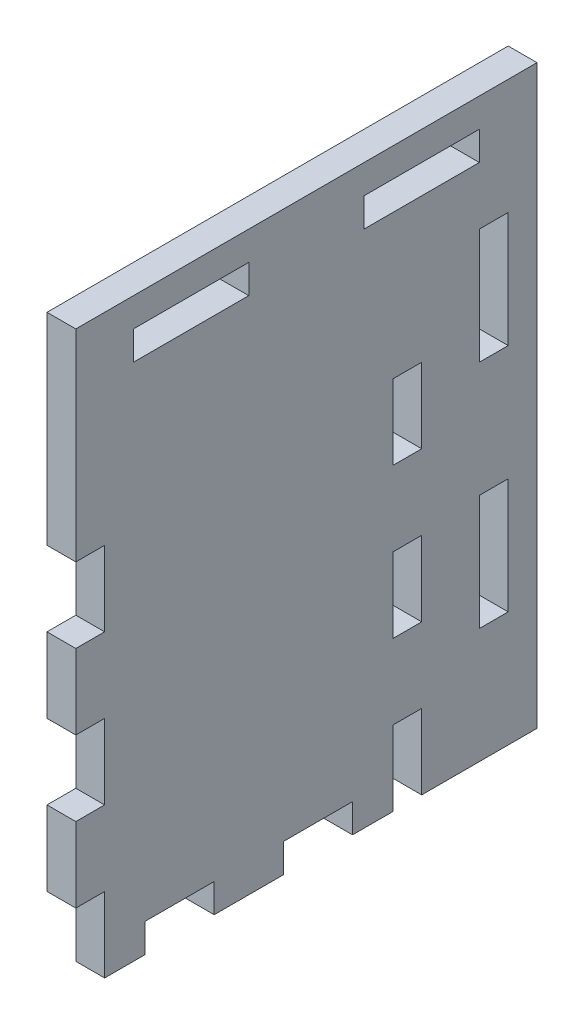
SolidWorks part; units mm, degrees
ref_plane "Plan de face" through (0, 0, 0) normal (0, 0, 1) x (1, 0, 0)
ref_plane "Plan de dessus" through (0, 0, 0) normal (0, 1, 0) x (1, 0, 0)
ref_plane "Plan de droite" through (0, 0, 0) normal (1, 0, 0) x (0, 0, -1)
sketch "Esquisse1" plane through (0, 0, 0) normal (1, 0, 0) x (0, 0, -1)
  line L0 (0, 0) -> (0, 35)
  line L2 (0, 0) -> (0, -65)
  line L3 (0, -65) -> (60, -65)
  line L4 (60, 0) -> (60, -65)
  line L5 (0, 35) -> (45, 35)
  line L7 (45, 0) -> (60, 0)
  line L8 (45, 0) -> (45, 35)
  dimension "D1" = 60
  dimension "D2" = 65
  dimension "D3" = 35
  dimension "D4" = 15
extrude "Boss.-Extru.1" add sketch "Esquisse1" along normal blind 5
sketch "Esquisse2" plane through (5, 0, 0) normal (1, 0, 0) x (0, 0, -1)
  line L0 (0, -65) -> (60, -65) construction
  line L1 (12, -65) -> (24, -65)
  line L2 (12, -65) -> (12, -60)
  line L3 (12, -60) -> (24, -60)
  line L4 (24, -65) -> (24, -60)
  line L5 (0, -65) -> (60, -65) construction
  line L6 (0, 35) -> (0, -65) construction
  dimension "D1" = 60
  dimension "D2" = 12
  dimension "D3" = 5
  dimension "D4" = 12
extrude "Enlèv. mat.-Extru.1" cut sketch "Esquisse2" against normal blind 5
pattern_linear "Répétition linéaire1" count 2 spacing 24 along (0, 0, -1) of "Enlèv. mat.-Extru.1"
ref_plane "Plan1" through (0, 0, -30) normal (0, 0, 1) x (1, 0, 0)
sketch "Esquisse4" plane through (5, 0, 0) normal (1, 0, 0) x (0, 0, -1)
  line L0 (60, 0) -> (60, -65) construction
  line L1 (0, -65) -> (5, -65)
  line L2 (0, -65) -> (0, -52)
  line L3 (0, -52) -> (5, -52)
  line L4 (5, -65) -> (5, -52)
  dimension "D3" = 5
  dimension "D1" = 65
  dimension "D2" = 13
extrude "Enlèv. mat.-Extru.2" cut sketch "Esquisse4" against normal blind 5
pattern_linear "Répétition linéaire2" count 3 spacing 26 along (0, 1, 0) of "Enlèv. mat.-Extru.2"
mirror "Symétrie1" about plane through (0, 0, -30) normal (0, 0, 1) of "Répétition linéaire2", "Enlèv. mat.-Extru.2"
sketch "Esquisse5" plane through (5, 0, 0) normal (1, 0, 0) x (0, 0, -1)
  line L0 (45, 0) -> (60, 0)
  line L2 (60, 0) -> (60, -65)
  line L3 (60, -65) -> (80, -65)
  line L5 (45, 0) -> (45, 35)
  line L6 (45, 35) -> (80, 35)
  line L8 (80, -65) -> (80, 35)
  line L9 (48, -65) -> (55, -65) construction
  line L10 (60, -52) -> (60, -39) construction
  dimension "D1" = 20
extrude "Boss.-Extru.3" add sketch "Esquisse5" against normal blind 5
ref_plane "Plan2" through (0, 0, -40) normal (0, 0, 1) x (1, 0, 0)
ref_plane "Plan3" through (0, -15, 0) normal (0, 1, 0) x (1, 0, 0)
sketch "Esquisse7" plane through (5, 0, 0) normal (1, 0, 0) x (0, 0, -1)
  line L1 (10, 30) -> (30, 30)
  line L2 (10, 30) -> (10, 25)
  line L3 (10, 25) -> (30, 25)
  line L4 (30, 30) -> (30, 25)
  line L5 (40, 2.75) -> (40, -2.75) construction
  line L6 (80, 35) -> (0, 35) construction
  line L7 (40, 35) -> (40, 10.2809) construction
  line L8 (50, 30) -> (50, 25)
  line L9 (70, 25) -> (50, 25)
  line L10 (70, 30) -> (70, 25)
  line L11 (70, 30) -> (50, 30)
  point P4 (30, 27.5)
  dimension "D1" = 20
  dimension "D2" = 5
  dimension "D3" = 10
  dimension "D4" = 5
extrude "Enlèv. mat.-Extru.3" cut sketch "Esquisse7" against normal blind 5
sketch "Esquisse8" plane through (5, 0, 0) normal (1, 0, 0) x (0, 0, -1)
  line L0 (2.75, -15) -> (-2.75, -15) construction
  line L1 (75, -5) -> (70, -5)
  line L2 (75, -5) -> (75, 15)
  line L3 (75, 15) -> (70, 15)
  line L4 (70, -5) -> (70, 15)
  line L5 (80, -65) -> (80, 35) construction
  line L6 (80, -15) -> (65.6039, -15) construction
  line L7 (70, -25) -> (70, -45)
  line L8 (75, -45) -> (70, -45)
  line L9 (75, -25) -> (75, -45)
  line L10 (75, -25) -> (70, -25)
  point P4 (72.5, -5)
  dimension "D1" = 20
  dimension "D2" = 5
  dimension "D3" = 10
  dimension "D4" = 5
extrude "Enlèv. mat.-Extru.4" cut sketch "Esquisse8" against normal blind 5
equation "\"D2@Esquisse2\"=\"D1@Esquisse2\"/5"
equation "\"D4@Esquisse2\"=\"D2@Esquisse2\""
equation "\"D2@Esquisse4\"=\"D1@Esquisse4\"/5"
equation "\"D3@Esquisse7\"=\"D1@Esquisse7\"/2"
equation "\"D3@Esquisse8\"=\"D1@Esquisse8\"/2"
